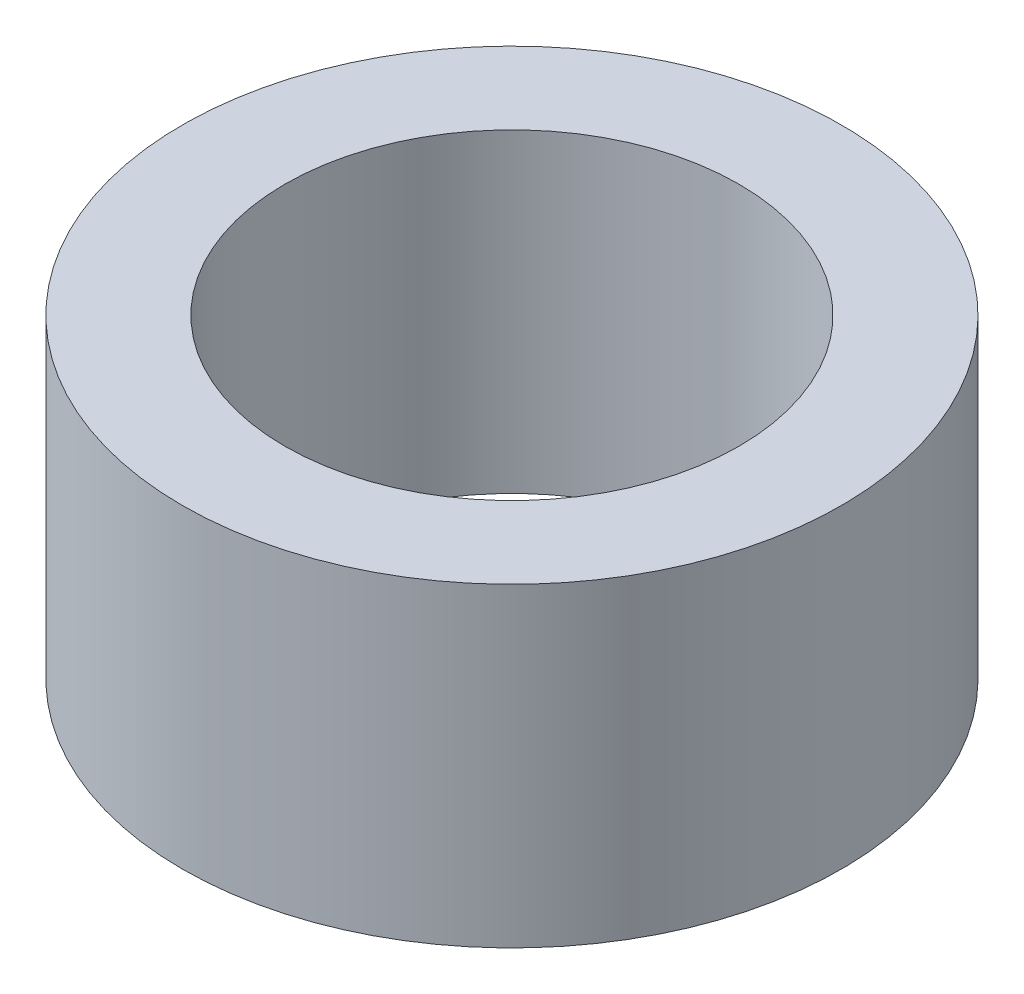
SolidWorks part; units mm, degrees
ref_plane "前视基准面" through (0, 0, 0) normal (0, 0, 1) x (1, 0, 0)
ref_plane "上视基准面" through (0, 0, 0) normal (0, 1, 0) x (1, 0, 0)
ref_plane "右视基准面" through (0, 0, 0) normal (1, 0, 0) x (0, 0, -1)
sketch "草图1" plane through (0, 0, 0) normal (0, 1, 0) x (1, 0, 0)
  circle A0 centre (0, 0) radius 3.1
  circle A1 centre (0, 0) radius 4.5
  dimension "D1" = 6.2
  dimension "D2" = 9
extrude "凸台-拉伸1" add sketch "草图1" along normal blind 4.3
